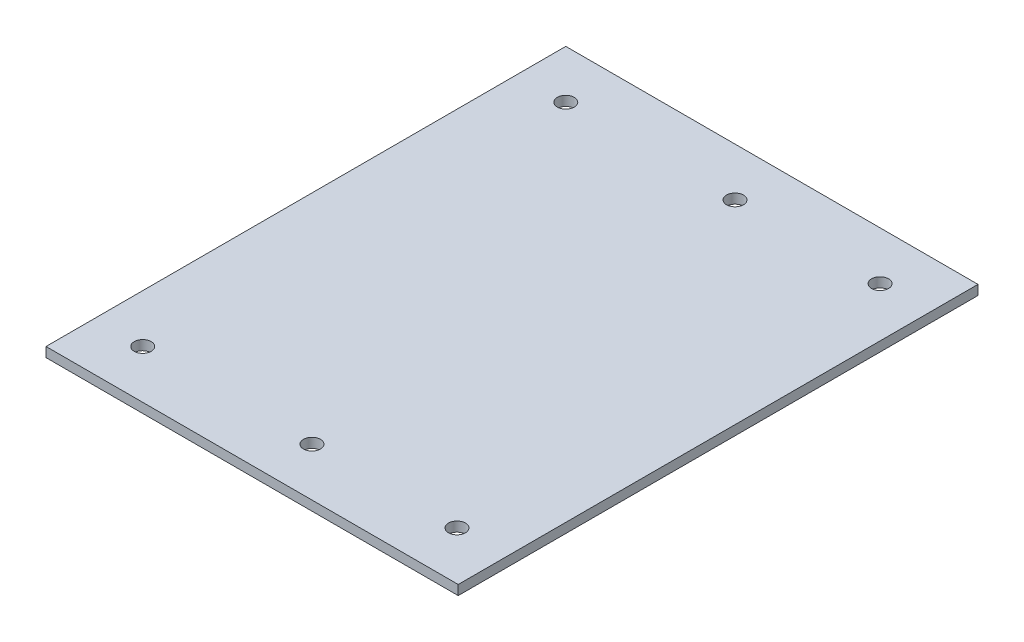
SolidWorks part; units mm, degrees
ref_plane "Front Plane" through (0, 0, 0) normal (0, 0, 1) x (1, 0, 0)
ref_plane "Top Plane" through (0, 0, 0) normal (0, 1, 0) x (1, 0, 0)
ref_plane "Right Plane" through (0, 0, 0) normal (1, 0, 0) x (0, 0, -1)
sketch "Sketch1" plane through (0, 0, 0) normal (0, 1, 0) x (1, 0, 0)
  line L1 (0, 205) -> (170.5, 205)
  line L2 (0, 205) -> (0, -10)
  line L3 (0, -10) -> (170.5, -10)
  line L4 (170.5, 205) -> (170.5, -10)
  circle A0 centre (20, 10) radius 3.5
  circle A1 centre (150, 10) radius 3.5
  circle A2 centre (90, 10) radius 3.5
  circle A3 centre (20, 185) radius 3.5
  circle A4 centre (90, 185) radius 3.5
  circle A5 centre (150, 185) radius 3.5
  point P16 (0, 0)
  point P17 (0, 0)
  point P18 (0, 0)
extrude "Boss-Extrude1" add sketch "Sketch1" along normal blind 4
